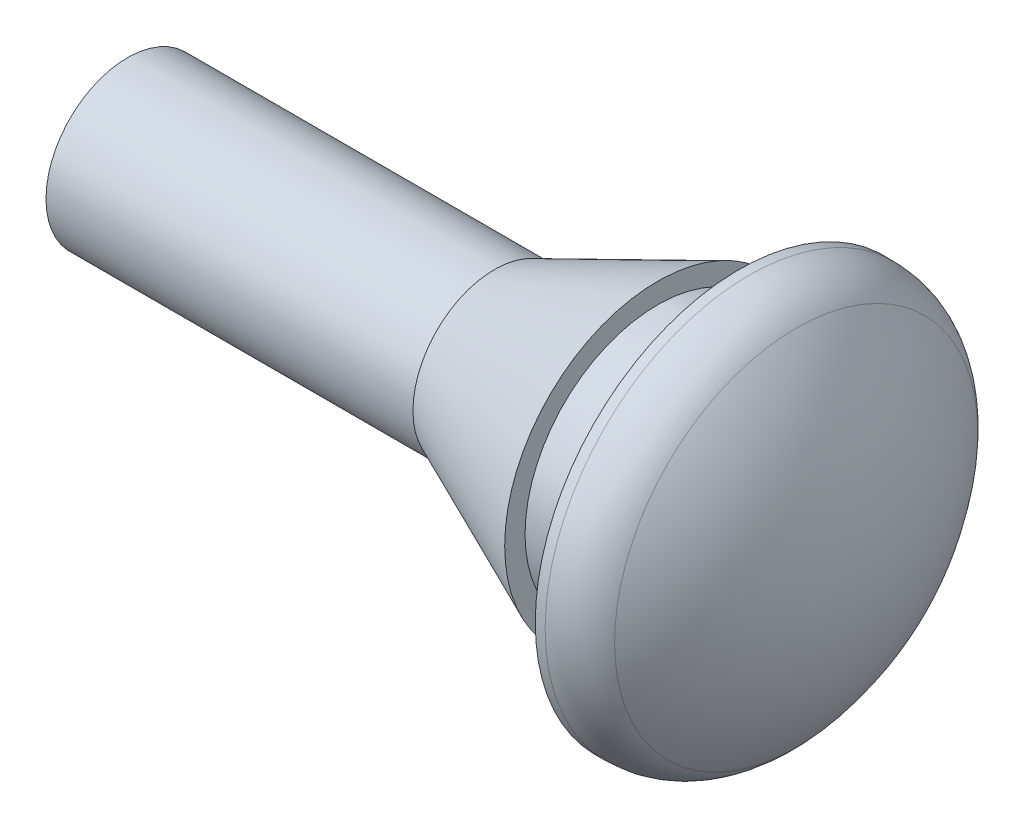
SolidWorks part; units mm, degrees
ref_plane "Plan de face" through (0, 0, 0) normal (0, 0, 1) x (1, 0, 0)
ref_plane "Plan de dessus" through (0, 0, 0) normal (0, 1, 0) x (1, 0, 0)
ref_plane "Plan de droite" through (0, 0, 0) normal (1, 0, 0) x (0, 0, -1)
sketch "Esquisse1" plane through (0, 0, 0) normal (0, 0, 1) x (1, 0, 0)
  line L0 (0, 0) -> (36.9141, 0) construction
  line L1 (0, 0) -> (-18, 0)
  line L2 (-18, 0) -> (-18, 2)
  line L3 (-18, 2) -> (-9, 2)
  line L4 (-9, 2) -> (-5, 3.75)
  line L5 (-5, 3.75) -> (-5, 3.25)
  line L6 (-5, 3.25) -> (-3, 3.25)
  line L7 (-3, 3.25) -> (-3, 5)
  line L8 (-3, 5) -> (-2.7574, 5)
  arc A0 (0, 0) -> (-1.6003, 4.4545) centre (-7, 0) ccw
  arc A1 (-1.6003, 4.4545) -> (-2.7574, 5) centre (-2.7574, 3.5) ccw
  dimension "D9" = 7
  dimension "D10" = 1.5
  dimension "D1" = 3
  dimension "D2" = 2
  dimension "D3" = 10
  dimension "D4" = 4
  dimension "D5" = 18
  dimension "D6" = 9
  dimension "D7" = 7.5
  dimension "D8" = 6.5
revolve "Révolution1" add sketch "Esquisse1" angle 360 about L0
